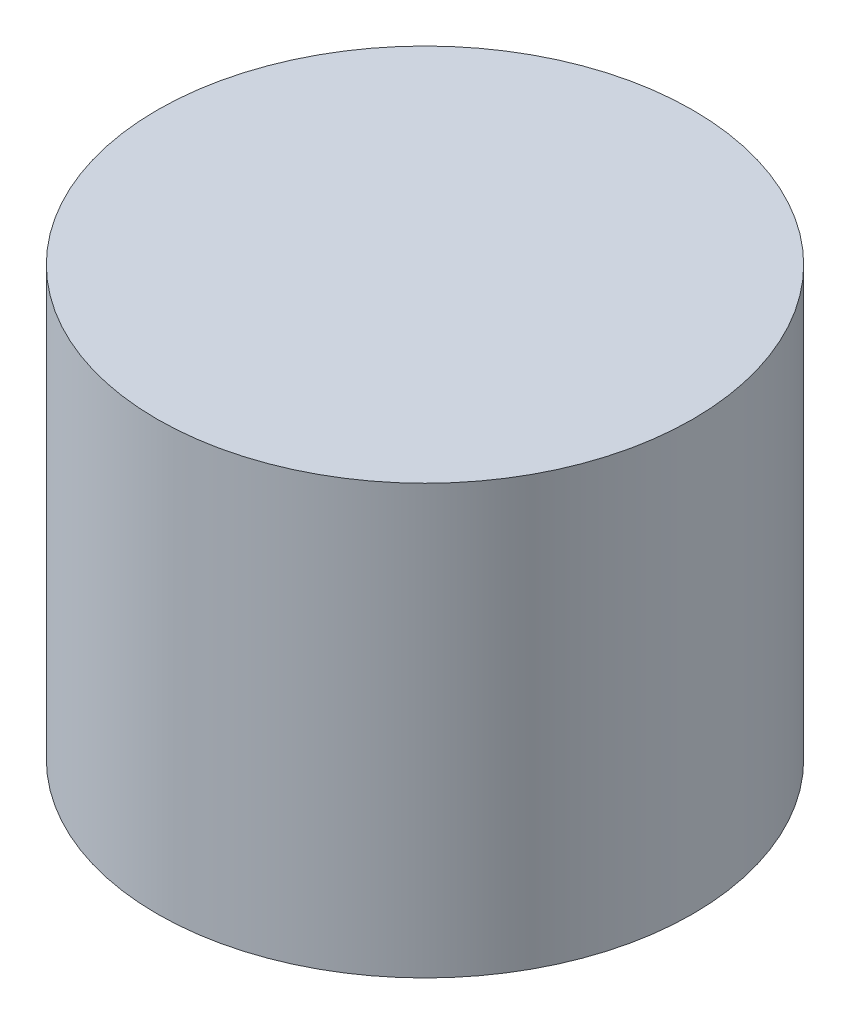
SolidWorks part; units mm, degrees
ref_plane "前视基准面" through (0, 0, 0) normal (0, 0, 1) x (1, 0, 0)
ref_plane "上视基准面" through (0, 0, 0) normal (0, 1, 0) x (1, 0, 0)
ref_plane "右视基准面" through (0, 0, 0) normal (1, 0, 0) x (0, 0, -1)
sketch "草图1" plane through (0, 0, 0) normal (0, 1, 0) x (1, 0, 0)
  circle A0 centre (0, 0) radius 2.5
  dimension "D1" = 5
extrude "凸台-拉伸1" add sketch "草图1" along normal blind 4
